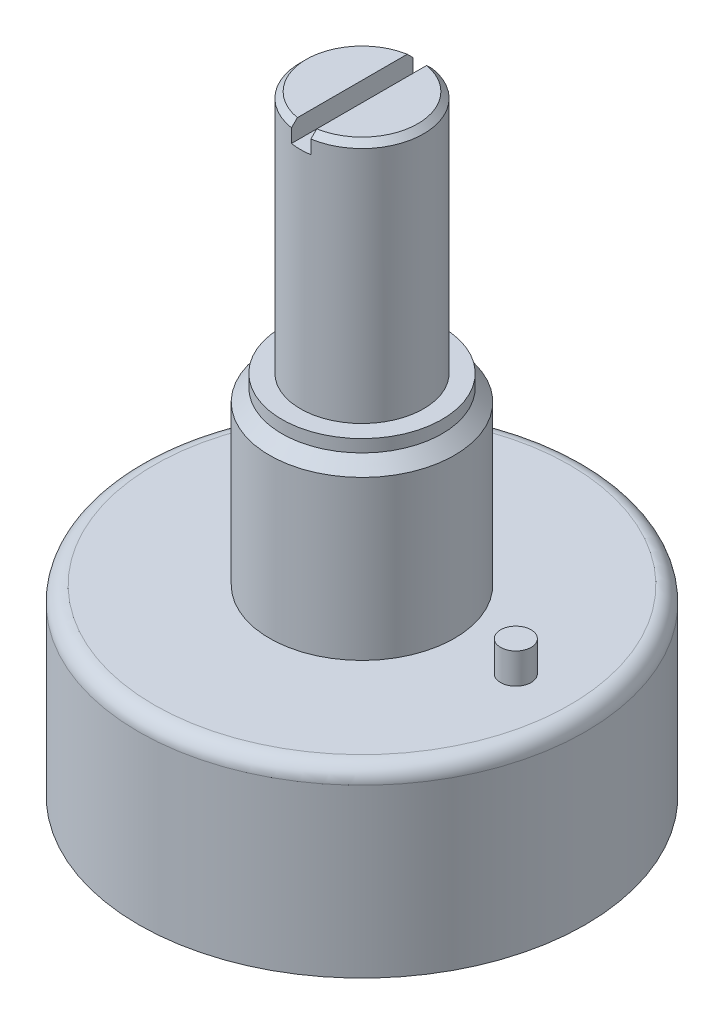
SolidWorks part; units mm, degrees
material "2014 Alloy High Density"
ref_plane "Front Plane" through (0, 0, 0) normal (0, 0, 1) x (1, 0, 0)
ref_plane "Top Plane" through (0, 0, 0) normal (0, 1, 0) x (1, 0, 0)
ref_plane "Right Plane" through (0, 0, 0) normal (1, 0, 0) x (0, 0, -1)
sketch "Sketch1" plane through (0, 0, 0) normal (0, 0, 1) x (1, 0, 0)
  line L0 (0, 0) -> (0, 31.4)
  line L1 (0, 31.4) -> (-3.1725, 31.4)
  line L2 (-3.1725, 31.4) -> (-3.1725, 18.84)
  line L3 (-3.1725, 18.84) -> (-4.1225, 18.84)
  line L4 (-4.1225, 18.84) -> (-4.1225, 18.2)
  line L5 (-4.1225, 18.2) -> (-4.7625, 17.56)
  line L6 (-4.7625, 17.56) -> (-4.7625, 9.4)
  line L7 (-4.7625, 9.4) -> (-11.5, 9.4)
  line L8 (-11.5, 9.4) -> (-11.5, 0)
  line L9 (-11.5, 0) -> (0, 0)
  dimension "D1" = 31.4
  dimension "D2" = 4.7625
  dimension "D3" = 3.1725
  dimension "D4" = 12.56
  dimension "D5" = 11.5
  dimension "D6" = 135
  dimension "D7" = 8.8
  dimension "D8" = 9.4
revolve "Revolve1" add sketch "Sketch1" angle 360 about L0
chamfer "Chamfer1" distance 0.3 angle 45 1 edges at (0, 31.4, -3.1725)
sketch "Sketch2" plane through (0, 31.4, 0) normal (0, 1, 0) x (1, 0, 0)
  line L1 (0.5, -3.286) -> (-0.5, -3.286)
  line L2 (0.5, -3.286) -> (0.5, 3.286)
  line L3 (0.5, 3.286) -> (-0.5, 3.286)
  line L4 (-0.5, -3.286) -> (-0.5, 3.286)
  line L5 (0.5, -3.286) -> (-0.5, 3.286) construction
  line L6 (0.5, 3.286) -> (-0.5, -3.286) construction
  point P0 (0, 0)
  dimension "D1" = 1
extrude "Cut-Extrude1" cut sketch "Sketch2" against normal blind 1
fillet "Fillet1" radius 0.8 1 edges at (0, 9.4, -11.5)
sketch "Sketch3" plane through (0, 9.4, 0) normal (0, 1, 0) x (1, 0, 0)
  circle A0 centre (7.92, 0) radius 0.785
  dimension "D1" = 1.57
  dimension "D2" = 7.92
extrude "Boss-Extrude1" add sketch "Sketch3" along normal blind 1.57
sketch "Sketch4" plane through (0, 0, 0) normal (0, -1, 0) x (1, 0, 0)
  line L0 (-3.182, 3.182) -> (0, 0)
  line L1 (0, 0) -> (-3.182, -3.182)
  line L2 (0, 0) -> (4.5, 0)
  circle A0 centre (4.5, 0) radius 1
  circle A1 centre (-3.182, 3.182) radius 1
  circle A2 centre (-3.182, -3.182) radius 1
  dimension "D1" = 2
  dimension "D2" = 2
  dimension "D3" = 2
  dimension "D4" = 0
  dimension "D5" = 4.5
  dimension "D6" = 4.5
  dimension "D7" = 4.5
  dimension "D8" = 90
  dimension "D9" = 135
extrude "Boss-Extrude2" add sketch "Sketch4" along normal blind 0.6
sketch "Sketch5" plane through (0, -0.6, 0) normal (0, -1, 0) x (1, 0, 0)
  circle A0 centre (-3.182, 3.182) radius 0.7
  circle A1 centre (4.5, 0) radius 0.7
  circle A2 centre (-3.182, -3.182) radius 0.7
extrude "Boss-Extrude3" add sketch "Sketch5" along normal blind 2
sketch "Sketch6" plane through (0, -2.6, 0) normal (0, -1, 0) x (1, 0, 0)
  circle A0 centre (-3.182, 3.182) radius 1
  circle A1 centre (4.5, 0) radius 1
  circle A2 centre (-3.182, -3.182) radius 1
extrude "Boss-Extrude4" add sketch "Sketch6" along normal blind 0.6
